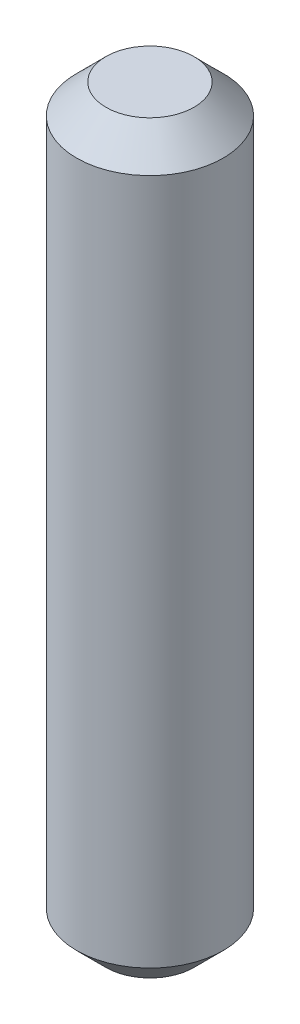
SolidWorks part; units mm, degrees
material "Cast Stainless Steel"
ref_plane "Front Plane" through (0, 0, 0) normal (0, 0, 1) x (1, 0, 0)
ref_plane "Top Plane" through (0, 0, 0) normal (0, 1, 0) x (1, 0, 0)
ref_plane "Right Plane" through (0, 0, 0) normal (1, 0, 0) x (0, 0, -1)
sketch "Sketch1" plane through (0, 0, 0) normal (0, 1, 0) x (1, 0, 0)
  circle A0 centre (0, 0) radius 1.25
  dimension "D1" = 2.5
extrude "Boss-Extrude1" add sketch "Sketch1" along normal blind 12.7
chamfer "Chamfer1" distance 0.5 angle 45 2 edges at (0, 0, 1.25) (0, 12.7, 1.25)
sketch3d "3DSketch1"
  line L0 (0, 0, 0) -> (0, 12.7, 0)
  line L1 (0, 12.2, 0) -> (0, 12.7, 0) construction
